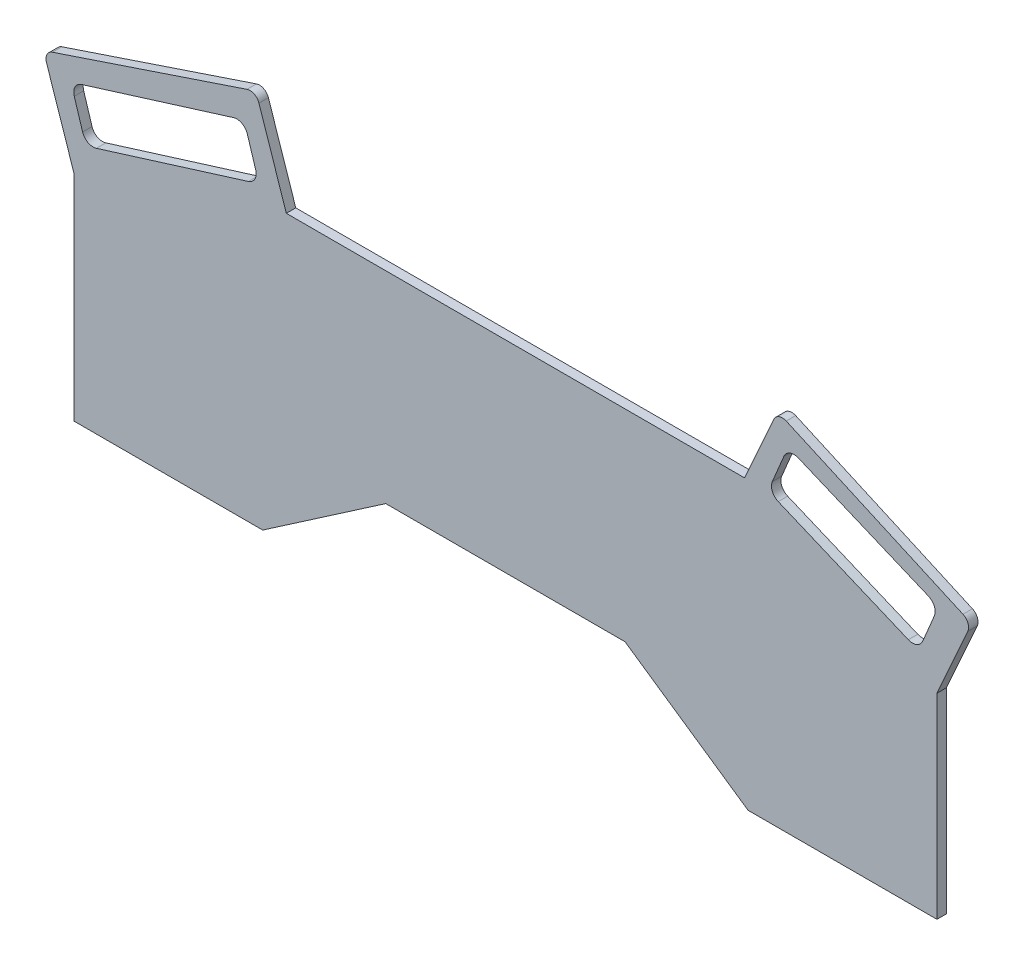
SolidWorks part; units mm, degrees
ref_plane "Front Plane" through (0, 0, 0) normal (0, 0, 1) x (1, 0, 0)
ref_plane "Top Plane" through (0, 0, 0) normal (0, 1, 0) x (1, 0, 0)
ref_plane "Right Plane" through (0, 0, 0) normal (1, 0, 0) x (0, 0, -1)
sketch "Sketch2" plane through (0, 0, 0) normal (0, 0, 1) x (1, 0, 0)
  line L0 (-257, -160) -> (-126.6944, -70.5678)
  line L1 (-457, -160) -> (-257, -160)
  line L2 (-457, -160) -> (-457, 67.6872)
  line L3 (-232, 143.0085) -> (253.3399, 143.0085)
  line L4 (457, -160) -> (457, 47.3657)
  line L5 (-457, -160) -> (319.5957, 111.8935) construction
  line L6 (-322.2114, 112.8092) -> (457, -160) construction
  line L7 (-126.6944, -70.5678) -> (126.6944, -70.5678)
  line L8 (126.6944, -70.5678) -> (257, -160)
  line L9 (257, -160) -> (457, -160)
  line L12 (253.3399, 143.0085) -> (284.209, 212.1378)
  line L13 (297.4173, 217.1914) -> (484.5653, 133.622)
  line L14 (489.619, 120.4136) -> (457, 47.3657)
  line L15 (-457, 67.6872) -> (-485.9821, 154.2628)
  line L16 (-479.6738, 166.92) -> (-273.6394, 235.8924)
  line L17 (-260.9821, 229.5841) -> (-232, 143.0085)
  arc A0 (489.619, 120.4136) -> (484.5653, 133.622) centre (480.488, 124.491) ccw
  arc A1 (297.4173, 217.1914) -> (284.209, 212.1378) centre (293.34, 208.0604) ccw
  arc A2 (-260.9821, 229.5841) -> (-273.6394, 235.8924) centre (-270.4649, 226.4096) ccw
  arc A3 (-479.6738, 166.92) -> (-485.9821, 154.2628) centre (-476.4994, 157.4372) ccw
  point P0 (0, 0)
  point P8 (0, -70.5678)
  point P21 (493.6963, 129.5446)
  point P28 (-489.1566, 163.7455)
  dimension "D9" = 10
  dimension "D1" = 914
  dimension "D2" = 225
  dimension "D3" = 200
  dimension "D4" = 225
  dimension "D5" = 90
  dimension "D6" = 90
  dimension "D7" = 90
  dimension "D8" = 101.2978
extrude "Boss-Extrude1" add sketch "Sketch2" along normal blind 10
sketch "Sketch3" plane through (0, 0, 10) normal (0, 0, 1) x (1, 0, 0)
  line L0 (-456.5681, 138.1281) -> (-447.7376, 109.7444)
  line L1 (-433.1356, 102.0722) -> (-272.1428, 152.1588)
  line L2 (-264.4705, 166.7608) -> (-273.301, 195.1445)
  line L3 (-287.903, 202.8167) -> (-448.8958, 152.7301)
  arc A0 (-272.1428, 152.1588) -> (-264.4705, 166.7608) centre (-275.6076, 163.2959) ccw
  arc A1 (-447.7376, 109.7444) -> (-433.1356, 102.0722) centre (-436.6005, 113.2093) ccw
  arc A2 (-273.301, 195.1445) -> (-287.903, 202.8167) centre (-284.4381, 191.6796) ccw
  arc A3 (-456.5681, 138.1281) -> (-448.8958, 152.7301) centre (-445.431, 141.5929) cw
  dimension "D1" = 11.6637
extrude "Cut-Extrude1" cut sketch "Sketch3" against normal blind 10
sketch "Sketch4" plane through (0, 0, 10) normal (0, 0, 1) x (1, 0, 0)
  line L0 (294.8897, 183.5051) -> (282.6677, 154.3604)
  line L1 (288.9132, 139.0936) -> (426.6793, 81.3207)
  line L2 (441.9461, 87.5662) -> (454.1681, 116.711)
  line L3 (447.9226, 131.9778) -> (310.1565, 189.7506)
  arc A0 (454.1681, 116.711) -> (447.9226, 131.9778) centre (443.412, 121.2216) ccw
  arc A1 (441.9461, 87.5662) -> (426.6793, 81.3207) centre (431.19, 92.0768) cw
  arc A2 (288.9132, 139.0936) -> (282.6677, 154.3604) centre (293.4239, 149.8497) cw
  arc A3 (294.8897, 183.5051) -> (310.1565, 189.7506) centre (305.6459, 178.9945) cw
  dimension "D1" = 11.6637
extrude "Cut-Extrude2" cut sketch "Sketch4" against normal blind 10
